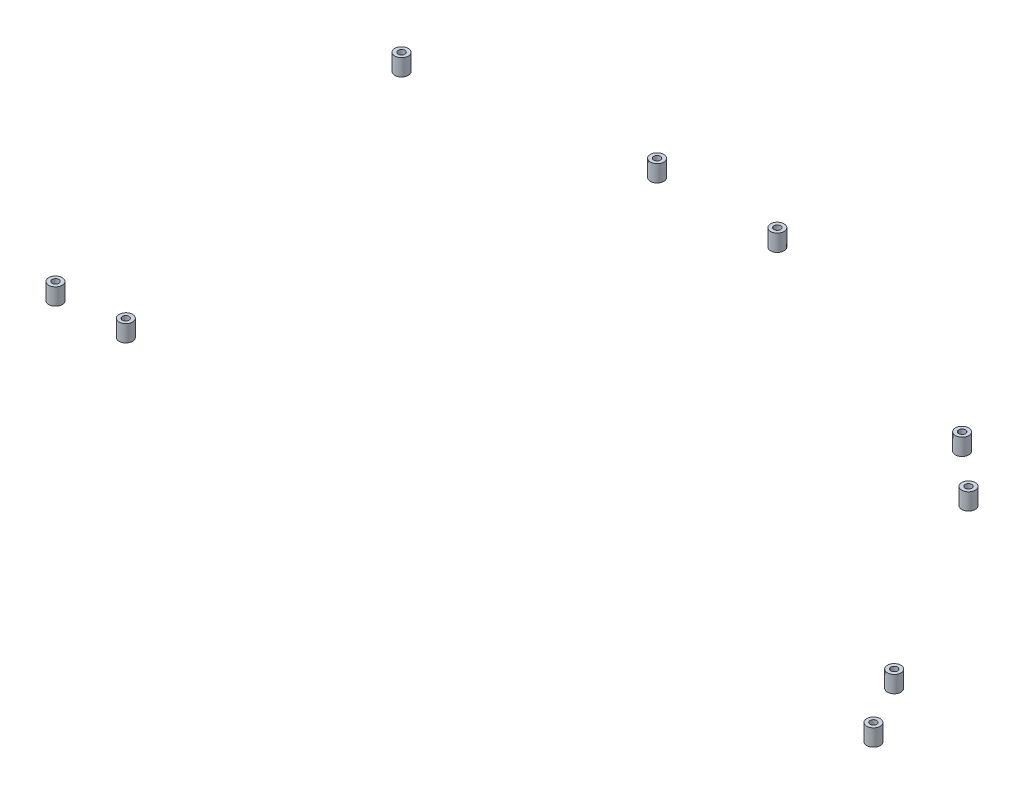
SolidWorks part; units mm, degrees
material "7075-O (SS)"
ref_plane "Płaszczyzna XY" through (0, 0, 0) normal (0, 0, 1) x (1, 0, 0)
ref_plane "Płaszczyzna XZ" through (0, 0, 0) normal (0, 1, 0) x (1, 0, 0)
ref_plane "Płaszczyzna YZ" through (0, 0, 0) normal (1, 0, 0) x (0, 0, -1)
sketch "Szkic1" plane through (0, 445, 0) normal (0, 1, 0) x (1, 0, 0)
  circle A0 centre (-572.688, -206.3657) radius 4
  circle A1 centre (-441.6637, -184.9064) radius 4
  circle A2 centre (-369.9079, -184.9064) radius 4
  circle A3 centre (-209.2942, -235.2328) radius 4
  circle A4 centre (-179.1662, -261.5446) radius 4
  circle A5 centre (-106.9414, -378.1441) radius 4
  circle A6 centre (-85.5135, -411.9205) radius 4
  circle A7 centre (-572.688, -206.3657) radius 2
  circle A8 centre (-441.6637, -184.9064) radius 2
  circle A9 centre (-369.9079, -184.9064) radius 2
  circle A10 centre (-209.2942, -235.2328) radius 2
  circle A11 centre (-179.1662, -261.5446) radius 2
  circle A12 centre (-106.9414, -378.1441) radius 2
  circle A13 centre (-85.5135, -411.9205) radius 2
  circle A14 centre (-557.5005, -428.0452) radius 2
  circle A15 centre (-517.5005, -426.1747) radius 2
  spline S2 degree 3 poles (-557.5005, -432.0764) (-549.5005, -432.0764) (-549.5005, -424.0764) (-557.5005, -424.0764) (-565.5005, -424.0764) (-565.5005, -432.0764) (-557.5005, -432.0764) (-549.5005, -432.0764) (-549.5005, -424.0764) knots -0.5 0 0 0 0.5 0.5 0.5 1 1 1 1.5 1.5 1.5 weights 1 0.333333 0.333333 1 0.333333 0.333333 1 0.333333 0.333333 only from (-557.5005, -432.0764) to (-557.5005, -432.0764)
  spline S3 degree 3 poles (-517.5005, -430.0794) (-509.5005, -430.0794) (-509.5005, -422.0794) (-517.5005, -422.0794) (-525.5005, -422.0794) (-525.5005, -430.0794) (-517.5005, -430.0794) (-509.5005, -430.0794) (-509.5005, -422.0794) knots -0.5 0 0 0 0.5 0.5 0.5 1 1 1 1.5 1.5 1.5 weights 1 0.333333 0.333333 1 0.333333 0.333333 1 0.333333 0.333333 only from (-517.5005, -430.0794) to (-517.5005, -430.0794)
  dimension "D1" = 4
  dimension "D2" = 4
  dimension "D3" = 4
  dimension "D4" = 4
  dimension "D5" = 4
  dimension "D6" = 4
  dimension "D7" = 4
  dimension "D8" = 4
  dimension "D9" = 4
extrude "Dodanie-wyciągnięcie1" add sketch "Szkic1" against normal blind 10
